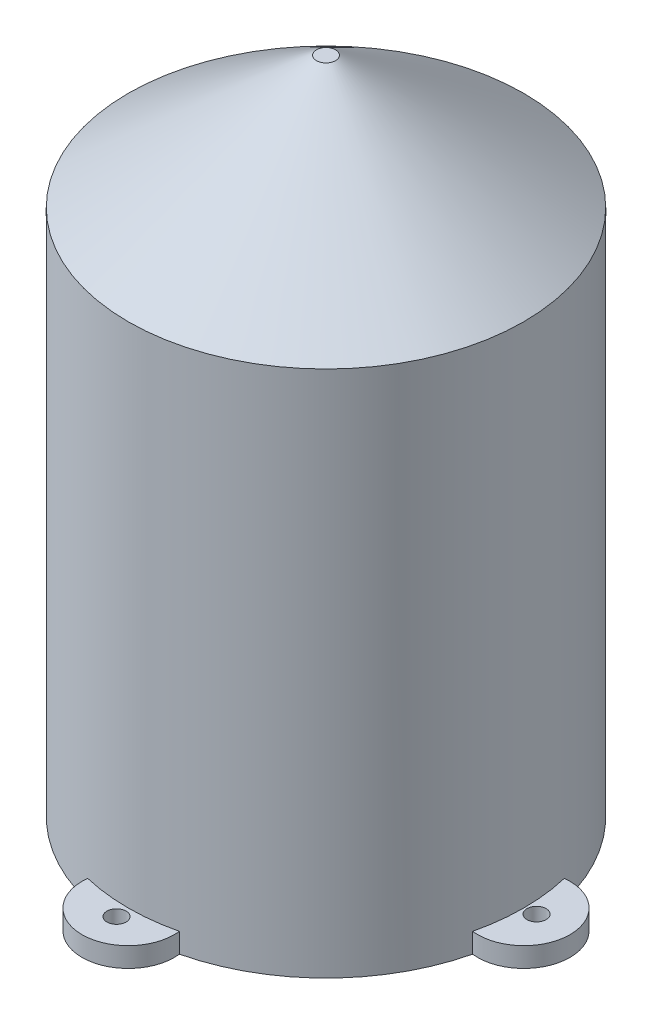
SolidWorks part; units mm, degrees
ref_plane "Front Plane" through (0, 0, 0) normal (0, 0, 1) x (1, 0, 0)
ref_plane "Top Plane" through (0, 0, 0) normal (0, 1, 0) x (1, 0, 0)
ref_plane "Right Plane" through (0, 0, 0) normal (1, 0, 0) x (0, 0, -1)
sketch "Sketch1" plane through (0, 0, 0) normal (0, 1, 0) x (1, 0, 0)
  circle A0 centre (0, 0) radius 30
  dimension "D1" = 60
extrude "Boss-Extrude1" add sketch "Sketch1" along normal blind 100
chamfer "Chamfer1" distance 20 angle 55 1 edges at (0, 100, 30)
shell "Shell1" thickness 2
sketch "Sketch2" plane through (0, 0, 0) normal (0, -1, 0) x (1, 0, 0)
  arc A0 (29.1833, 6.9522) -> (29.1833, -6.9522) centre (30, 0) cw
  circle A1 centre (0, 0) radius 30 construction
  circle A2 centre (0, 0) radius 30
  arc A3 (6.9522, -29.1833) -> (-6.9522, -29.1833) centre (0, -30) cw
  arc A4 (-29.1833, -6.9522) -> (-29.1833, 6.9522) centre (-30, 0) cw
  arc A5 (-6.9522, 29.1833) -> (6.9522, 29.1833) centre (0, 30) cw
  point P19 (0, 0)
  circle M2 centre (0, 0) radius 30
  dimension "D1" = 7
  dimension "D2" = 4
extrude "Boss-Extrude2" add sketch "Sketch2" against normal blind 3 contours A0 M2 | A5 A2 | A4 A2 | A3 A2
hole_wizard "Ø1.0mm Dowel Hole1" positions "3DSketch1" profile "Sketch4" hole size "Ø1.0" standard "ANSI Metric"
sketch3d "3DSketch1"
  point P0 (0.2389, 0, 32.0083)
  point P2 (31.7694, 0, -0.1592)
  point P4 (-0.2389, 0, -32.9637)
  point P6 (-32.7249, 0, -0.3185)
sketch "Sketch4" plane through (0.2389, 0, 32.0083) normal (1, 0, 0) x (0, 0, -1)
  line L0 (0, 0) -> (0, 10)
  line L1 (0, 10) -> (1.45, 9.1288)
  line L2 (1.45, 9.1288) -> (1.45, 0)
  line L5 (1.45, 0) -> (0, 0)
  line L10 (0, 10) -> (-1.45, 9.1288) construction
  line L11 (0, -6.35) -> (0, 107.95) construction
  dimension "Hole Dia." = 2.9
  dimension "Hole Depth" = 10
  dimension "Drill Angle" = 118
